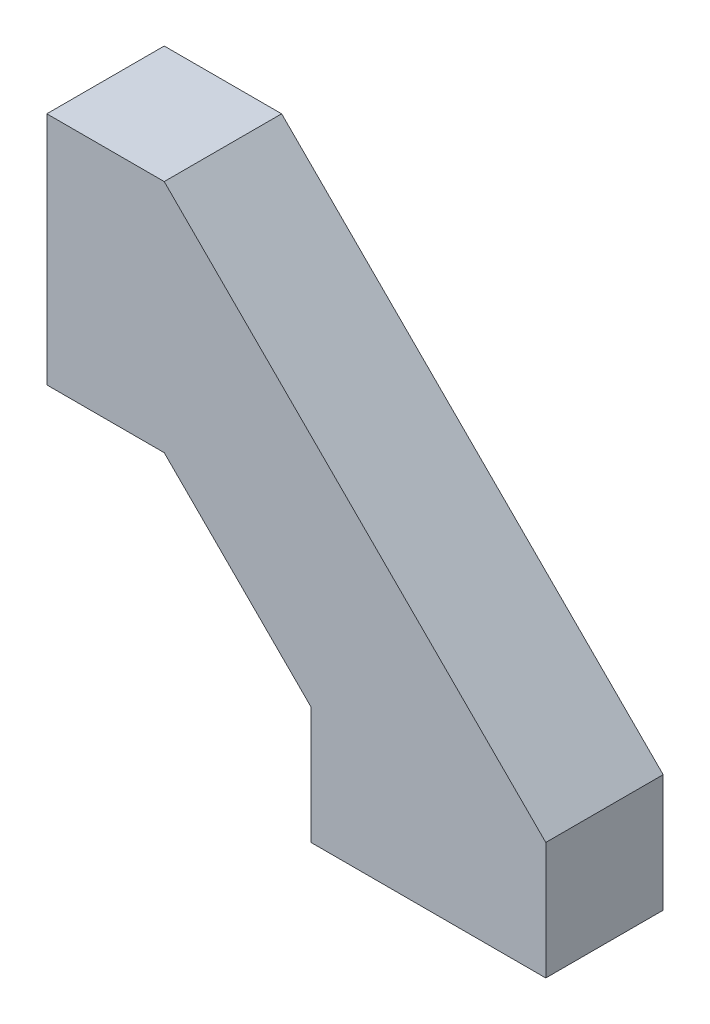
SolidWorks part; units mm, degrees
ref_plane "Front Plane" through (0, 0, 0) normal (0, 0, 1) x (1, 0, 0)
ref_plane "Top Plane" through (0, 0, 0) normal (0, 1, 0) x (1, 0, 0)
ref_plane "Right Plane" through (0, 0, 0) normal (1, 0, 0) x (0, 0, -1)
sketch "Sketch1" plane through (0, 0, 0) normal (0, 0, 1) x (1, 0, 0)
  line L0 (-8, 4) -> (-13, 9)
  line L1 (0, 0) -> (-8, 0)
  line L2 (0, 0) -> (0, 4)
  line L3 (0, 4) -> (-8, 4)
  line L4 (-8, 0) -> (-8, 4)
  line L5 (0, 4) -> (-5, 9)
  line L6 (-13, 9) -> (-5, 9)
  line L7 (-13, 9) -> (-13, 17)
  line L8 (-5, 9) -> (-17, 9)
  line L11 (-17, 9) -> (-17, 17)
  line L13 (-17, 17) -> (-17, 9)
  line L14 (-17, 9) -> (-5, 9)
  line L16 (-17, 17) -> (-13, 17)
  line L17 (-5, 9) -> (-13, 17)
  dimension "D1" = 8
  dimension "D2" = 4
  dimension "D3" = 5
  dimension "D4" = 4
  dimension "D5" = 8
  dimension "D6" = 135
extrude "Boss-Extrude1" add sketch "Sketch1" along normal blind 4
